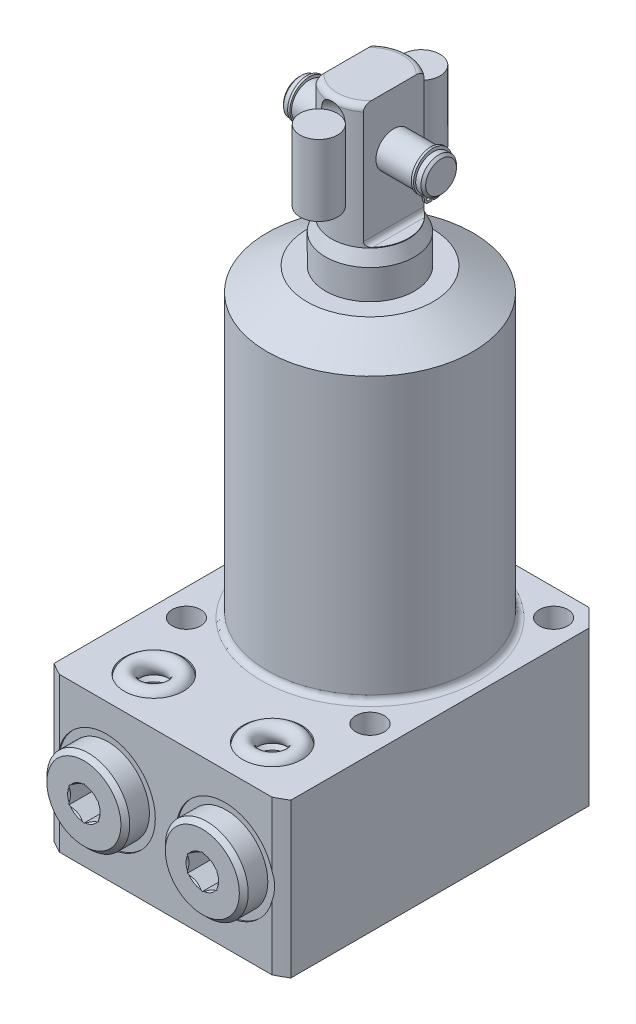
SolidWorks part; units mm, degrees
material "AISI 1020"
ref_plane "Front Plane" through (0, 0, 0) normal (0, 0, 1) x (1, 0, 0)
ref_plane "Top Plane" through (0, 0, 0) normal (0, 1, 0) x (1, 0, 0)
ref_plane "Right Plane" through (0, 0, 0) normal (1, 0, 0) x (0, 0, -1)
sketch "Sketch1" plane through (0, 0, 0) normal (0, 0, 1) x (1, 0, 0)
  line L0 (7.5, 0) -> (7.5, 56.5)
  line L1 (7.5, 56.5) -> (6.5, 58.6445)
  line L2 (6.5, 58.6445) -> (6.5, 78.5)
  line L3 (5.5, 79.5) -> (0, 79.5)
  line L4 (0, 61.9815) -> (0, 93.5758) construction
  line L8 (0, -3.075) -> (0, 64.575) construction
  line L9 (7.5, 0) -> (0, 0)
  line L10 (0, 0) -> (0, 79.5)
  line L11 (-25.0821, -26) -> (21.8096, -26) construction
  arc A0 (6.5, 78.5) -> (5.5, 79.5) centre (5.5, 78.5) ccw
  dimension "D1" = 1
  dimension "D2" = 15
  dimension "D3" = 13
  dimension "D4" = 23
  dimension "D5" = 26
  dimension "D6" = 25
  dimension "D7" = 105.5
revolve "PLUNGER" add sketch "Sketch1" angle 360 about L8
ref_plane "FLAT_SKTCH_PLN" through (0, 0, 0) normal (0, 0, 1) x (1, 0, 0)
sketch "Sketch17" plane through (0, 0, 0) normal (0, 0, 1) x (1, 0, 0)
  line L0 (5.5, 79.5) -> (-5.5, 79.5) construction
  line L1 (6.5, 58.6445) -> (6.5, 78.5) construction
  line L2 (5.5, 79.5) -> (-5.5, 79.5)
  line L3 (6.5, 58.6445) -> (6.5, 78.5)
  line L5 (4, 79.5) -> (6.5, 79.5)
  line L6 (4, 79.5) -> (4, 59.55)
  line L7 (4.8, 58.75) -> (6.5, 58.75)
  line L8 (6.5, 79.5) -> (6.5, 58.75)
  line L9 (0, 78.5) -> (0, 58.6445) construction
  line L10 (0, 57.0947) -> (0, 92.2162) construction
  line L11 (0, 56.5) -> (0, 0) construction
  line L12 (0, 56.5) -> (0, 58.6445) construction
  line L13 (-6.5, 79.5) -> (-6.5, 58.75)
  line L14 (-4.8, 58.75) -> (-6.5, 58.75)
  line L15 (-4, 79.5) -> (-4, 59.55)
  line L16 (-4, 79.5) -> (-6.5, 79.5)
  line L17 (-6.5, 58.6445) -> (-6.5, 78.5)
  arc A0 (4, 59.55) -> (4.8, 58.75) centre (4.8, 59.55) ccw
  arc A1 (-4, 59.55) -> (-4.8, 58.75) centre (-4.8, 59.55) cw
  dimension "D3" = 0.8
  dimension "D1" = 20.75
  dimension "D2" = 8
extrude "FLATS" cut sketch "Sketch17" against normal mid plane 100 contours L6 A0 L7 L8 L5 | L13 L14 A1 L15 L16
sketch "Sketch22" plane through (0, 0, 0) normal (0, 0, 1) x (1, 0, 0)
  line L0 (-11.5689, 70.5) -> (12.3381, 70.5) construction
  line L1 (0, 87.9433) -> (0, 65.5754) construction
  line L2 (0, 80.708) -> (0, 75.584) construction
  line L3 (0, 78.5) -> (0, 58.6445) construction
  line L4 (4, 79.5) -> (-4, 79.5) construction
  line L5 (4, 79.5) -> (-4, 79.5)
  line L6 (12, 73.1) -> (11.6, 73.5)
  line L7 (11.6, 73.5) -> (10.71, 73.5)
  line L8 (12, 73.1) -> (12, 70.5)
  line L9 (12, 70.5) -> (-12, 70.5)
  line L11 (10.71, 73.5) -> (10.71, 73.32)
  line L12 (10.71, 73.32) -> (10.25, 73.32)
  line L13 (10.25, 73.32) -> (10.25, 73.5)
  line L14 (10.25, 73.5) -> (-10.25, 73.5)
  line L15 (-10.25, 73.32) -> (-10.25, 73.5)
  line L16 (-10.71, 73.32) -> (-10.25, 73.32)
  line L17 (-10.71, 73.5) -> (-10.71, 73.32)
  line L18 (-12, 73.1) -> (-12, 70.5)
  line L19 (-11.6, 73.5) -> (-10.71, 73.5)
  line L20 (-12, 73.1) -> (-11.6, 73.5)
  dimension "D1" = 9
  dimension "D2" = 45
  dimension "D3" = 0.4
  dimension "D4" = 6
  dimension "D5" = 0.46
  dimension "D6" = 5.64
  dimension "D7" = 24
  dimension "D8" = 20.5
revolve "PIVOT_PIN" add sketch "Sketch22" angle 360 about L0
sketch "Sketch23" plane through (10.25, 0, 0) normal (1, 0, 0) x (0, 0, -1)
  line L0 (0, 79.466) -> (0, 70.8639) construction
  line L1 (0, 78.5) -> (0, 58.6445) construction
  line L2 (0, 70.5) -> (-2.4912, 67.0158) construction
  line L3 (-0.1775, 66.3558) -> (-0.76, 66.3558)
  line L4 (0, 70.5) -> (2.4912, 67.0158) construction
  line L5 (0.1775, 67.7758) -> (0.1775, 66.3558)
  line L6 (-0.1775, 67.7758) -> (-0.1775, 66.3558)
  line L7 (0.1775, 66.3558) -> (0.76, 66.3558)
  arc A0 (0.1775, 67.7758) -> (-0.1775, 67.7758) centre (0, 70.5) ccw
  arc A1 (-1.42, 67.0158) -> (-0.76, 66.3558) centre (-0.76, 67.0158) ccw
  arc A2 (-1.42, 67.0158) -> (-1.8682, 67.8872) centre (-2.4912, 67.0158) ccw
  arc A3 (-1.8682, 67.8872) -> (0, 73.992) centre (0.0902, 70.6261) cw
  circle A4 centre (-0.76, 67.0158) radius 0.33
  circle A5 centre (0.76, 67.0158) radius 0.33
  arc A6 (1.8682, 67.8872) -> (0, 73.992) centre (-0.0902, 70.6261) ccw
  arc A7 (1.42, 67.0158) -> (1.8682, 67.8872) centre (2.4912, 67.0158) cw
  arc A8 (1.42, 67.0158) -> (0.76, 66.3558) centre (0.76, 67.0158) cw
  point P17 (-1.5878, 68.2793)
  point P27 (1.5878, 68.2793)
  point P28 (0, 73.23)
  dimension "D1" = 5.46
  dimension "D3" = 0.66
  dimension "D8" = 0.66
  dimension "D2" = 0.355
  dimension "D4" = 1.42
  dimension "D5" = 1.42
  dimension "D6" = 0.762
  dimension "D7" = 0.482
extrude "RETAINING_RING" add sketch "Sketch23" along normal blind 0.381
ref_plane "PIN_CL" through (0, 0, 0) normal (-1, 0, 0) x (0, 0, 1)
mirror "RETAINING_RING-OPP" about plane through (0, 0, 0) normal (-1, 0, 0) of "RETAINING_RING"
sketch "Sketch20" plane through (0, 0, 0) normal (-1, 0, 0) x (0, 0, 1)
  line L0 (-3.7749, 79.5) -> (3.7749, 79.5) construction
  line L1 (-3.7749, 79.5) -> (3.7749, 79.5)
  line L2 (0, 87.5232) -> (0, 65.9324) construction
  line L3 (0, 80.7086) -> (0, 75.5829) construction
  line L4 (0, 78.5) -> (0, 58.6445) construction
  line L5 (8.675, 86.548) -> (8.675, 59.3595) construction
  line L6 (5.5, 76.5) -> (5.5, 64.5)
  line L7 (8.675, 79.675) -> (8.675, 61.325)
  arc A0 (8.675, 79.675) -> (5.5, 76.5) centre (8.675, 76.5) ccw
  arc A1 (5.5, 64.5) -> (8.675, 61.325) centre (8.675, 64.5) ccw
  dimension "D3" = 12
  dimension "D1" = 5.5
  dimension "D2" = 6.35
  dimension "D4" = 3
revolve "SPRING_SLOT" cut sketch "Sketch20" angle 360 about L5
mirror "SPRING_SLOT_OPP" about plane through (0, 0, 0) normal (0, 0, 1) of "SPRING_SLOT"
sketch "Sketch24" plane through (0, 0, 0) normal (-1, 0, 0) x (0, 0, 1)
  line L0 (7.2759, 70.5) -> (-10.8708, 70.5) construction
  line L1 (-8.645, 84.5678) -> (-8.645, 68.6953) construction
  line L2 (-5.5, 64.5) -> (-5.5, 76.5) construction
  line L3 (-5.47, 76.5) -> (-8.645, 76.5)
  line L4 (-5.47, 76.5) -> (-5.47, 64.5)
  line L6 (-8.645, 76.5) -> (-8.645, 64.5)
  line L7 (-5.47, 64.5) -> (-8.645, 64.5)
  dimension "D1" = 6.35
  dimension "D2" = 12
  dimension "D3" = 0.03
revolve "SPRING" add sketch "Sketch24" angle 360 about L1
mirror "SPRING_OPP" about plane through (0, 0, 0) normal (0, 0, 1) of "SPRING"
sketch "Sketch6" plane through (0, 0, 0) normal (0, 0, 1) x (1, 0, 0)
  line L0 (0, -26) -> (0, 67.6291) construction
  line L1 (0, 51.5) -> (10.625, 51.5)
  line L2 (10.625, 51.5) -> (17.385, 47.5971)
  line L3 (38.895, 0) -> (38.895, -26)
  line L4 (0, -26) -> (38.895, -26)
  line L5 (17.385, 0) -> (17.385, 47.5971)
  line L6 (38.895, 0) -> (17.385, 0)
  line L7 (0, -26) -> (0, 51.5)
  dimension "D1" = 34.77
  dimension "D2" = 26
  dimension "D3" = 77.5
  dimension "D4" = 77.79
  dimension "D5" = 30
  dimension "D6" = 21.25
revolve "BODY_REVOLVE" add sketch "Sketch6" angle 360 about L0
sketch "Sketch7" plane through (0, 0, 0) normal (0, 1, 0) x (-1, 0, 0)
  line L0 (0, 0) -> (0, -52.3237) construction
  line L1 (-20, 34.5) -> (20, 34.5)
  line L2 (-20, 34.5) -> (-20, -20)
  line L3 (-20, -20) -> (20, -20)
  line L4 (20, 34.5) -> (20, -20)
  dimension "D1" = 40
  dimension "D2" = 54.5
  dimension "D3" = 20
extrude "FLANGE_SIDES" cut sketch "Sketch7" against normal through all flip side to cut
sketch "Sketch8" plane through (0, -26, 0) normal (0, -1, 0) x (1, 0, 0)
  circle A0 centre (-15.5, 15.5) radius 2.4
  dimension "D1" = 4.8
  dimension "D2" = 15.5
  dimension "D3" = 15.5
extrude "MOUNTING HOLES" cut sketch "Sketch8" against normal through all
pattern_circular "MOUNTING_PATTERN" count 4 over 360 about axis through (0, 0, 0) along (0, 1, 0) of "MOUNTING HOLES"
chamfer "FLANGE_CHAMFER" distance 3 angle 45 2 edges at (-20, -13, -20) (20, -13, -20)
fillet "BODY_FILLET" radius 1 1 edges at (0, 0, -17.385)
ref_plane "FLANGE-PORT_PLANE" through (0, -13, 0) normal (0, -1, 0) x (1, 0, 0)
sketch "Sketch11" plane through (0, -13, 0) normal (0, -1, 0) x (1, 0, 0)
  line L0 (-10, 42.9716) -> (-10, 19.7499) construction
  line L1 (-18.25, 34.5) -> (-18.25, 34.25)
  line L3 (-18.25, 34.25) -> (-15, 34.25)
  line L4 (-15, 34.25) -> (-14.42, 33.67)
  line L5 (-14.42, 33.67) -> (-14.42, 19.09)
  line L6 (-14.42, 19.09) -> (-10, 19.09)
  line L7 (-10, 19.09) -> (-10, 34.5)
  line L8 (-10, 34.5) -> (-18.25, 34.5)
  line L10 (17.9603, 34.5) -> (-17.9603, 34.5) construction
  dimension "D1" = 10
  dimension "D2" = 0.25
  dimension "D3" = 8.84
  dimension "D4" = 15.16
  dimension "D5" = 16.5
  dimension "D6" = 45
  dimension "D7" = 0.58
revolve "PORT SPOT FACE" cut sketch "Sketch11" angle 360 about L0
ref_plane "MANIFOLD_PORT_PLANE" through (0, 0, 26.5) normal (0, 0, 1) x (1, 0, 0)
sketch "Sketch13" plane through (0, 0, 26.5) normal (0, 0, 1) x (1, 0, 0)
  line L0 (-12.5, -14) -> (-12.5, -23.125)
  line L1 (-12.5, -23.125) -> (-13.125, -23.75)
  line L2 (-13.125, -23.75) -> (-15, -23.75)
  line L3 (-15, -23.75) -> (-15, -26)
  line L5 (-15, -26) -> (-10, -26)
  line L6 (-10, -26) -> (-10, -14)
  line L7 (-10, -14) -> (-12.5, -14)
  line L8 (-10, 15.2099) -> (-10, -4.3918) construction
  line L10 (17.9603, -26) -> (-17.9603, -26) construction
  dimension "D1" = 10
  dimension "D2" = 5
  dimension "D3" = 12
  dimension "D4" = 2.25
  dimension "D5" = 10
  dimension "D6" = 45
  dimension "D7" = 0.625
revolve "BOTTOM_MANIFOLD_PORT" cut sketch "Sketch13" angle 360 about L8
sketch "Sketch14" plane through (0, -13, 0) normal (0, -1, 0) x (1, 0, 0)
  line L0 (-10, 32.5881) -> (-10, 43.3353) construction
  line L1 (-10, 19.09) -> (-10, 33.67) construction
  line L2 (-12.75, 38.31) -> (-16.25, 38.31)
  line L3 (-16.25, 38.31) -> (-17, 37.56)
  line L4 (-17, 37.56) -> (-17, 34.25)
  line L5 (-1.75, 34.25) -> (-18.25, 34.25) construction
  line L6 (-17, 34.25) -> (-14.125, 34.25)
  line L7 (-5, 34.25) -> (-15, 34.25) construction
  line L8 (-14.125, 34.25) -> (-14.125, 31.8078)
  line L9 (-14.125, 31.8078) -> (-10, 31.8078)
  line L10 (-10, 31.8078) -> (-10, 31.8088)
  line L11 (-10, 31.8088) -> (-12.5, 33.311)
  line L12 (-12.5, 33.311) -> (-12.5, 38.06)
  line L13 (-12.5, 38.06) -> (-12.75, 38.31)
  dimension "D1" = 8.25
  dimension "D2" = 2.4422
  dimension "D3" = 59
  dimension "D4" = 5
  dimension "D5" = 4.06
  dimension "D6" = 14
  dimension "D7" = 45
  dimension "D8" = 0.75
  dimension "D9" = 45
  dimension "D10" = 0.25
  dimension "D11" = 0.001
revolve "BSPP_PLUGHEAD" add sketch "Sketch14" angle 360 about L0
sketch "Sketch15" plane through (0, 0, 38.31) normal (0, 0, 1) x (1, 0, 0)
  line L1 (-7.5, -14.4434) -> (-7.5, -11.5566)
  line L2 (-7.5, -11.5566) -> (-10, -10.1132)
  line L3 (-10, -10.1132) -> (-12.5, -11.5566)
  line L4 (-12.5, -11.5566) -> (-12.5, -14.4434)
  line L5 (-12.5, -14.4434) -> (-10, -15.8868)
  line L6 (-10, -15.8868) -> (-7.5, -14.4434)
  circle A0 centre (-10, -13) radius 2.5 construction
  dimension "D1" = 5
extrude "BSPP_PLUG_HEX" cut sketch "Sketch15" against normal blind 4.06
mirror "MANIFOLD_TOP_MIRROR" about plane through (0, -13, 0) normal (0, -1, 0) of "BOTTOM_MANIFOLD_PORT"
mirror "BSPP-MANIFOLD_MIRROR" about plane through (0, 0, 0) normal (1, 0, 0) of "MANIFOLD_TOP_MIRROR", "PORT SPOT FACE", "BOTTOM_MANIFOLD_PORT", "BSPP_PLUGHEAD", "BSPP_PLUG_HEX"
sketch "Sketch16" plane through (0, 0, 26.5) normal (0, 0, 1) x (1, 0, 0)
  line L1 (-10, 9.3219) -> (-10, -15.1063) construction
  line L2 (-10, -23.125) -> (-10, -16.6451) construction
  line L3 (17.9603, -26) -> (-17.9603, -26) construction
  circle A0 centre (-13.5, -25.25) radius 1.5
  dimension "D1" = 3
  dimension "D3" = 0.75
  dimension "D2" = 7
revolve "MANIFOLD_O-RING" add sketch "Sketch16" angle 360 about L1
mirror "MANIFOLD_O-RING_MIRROR" about plane through (0, 0, 0) normal (1, 0, 0) of bodies 128
mirror "MANIFOLD_O-RING_MIRROR_TOP" about plane through (0, -13, 0) normal (0, -1, 0) of bodies 128 130
